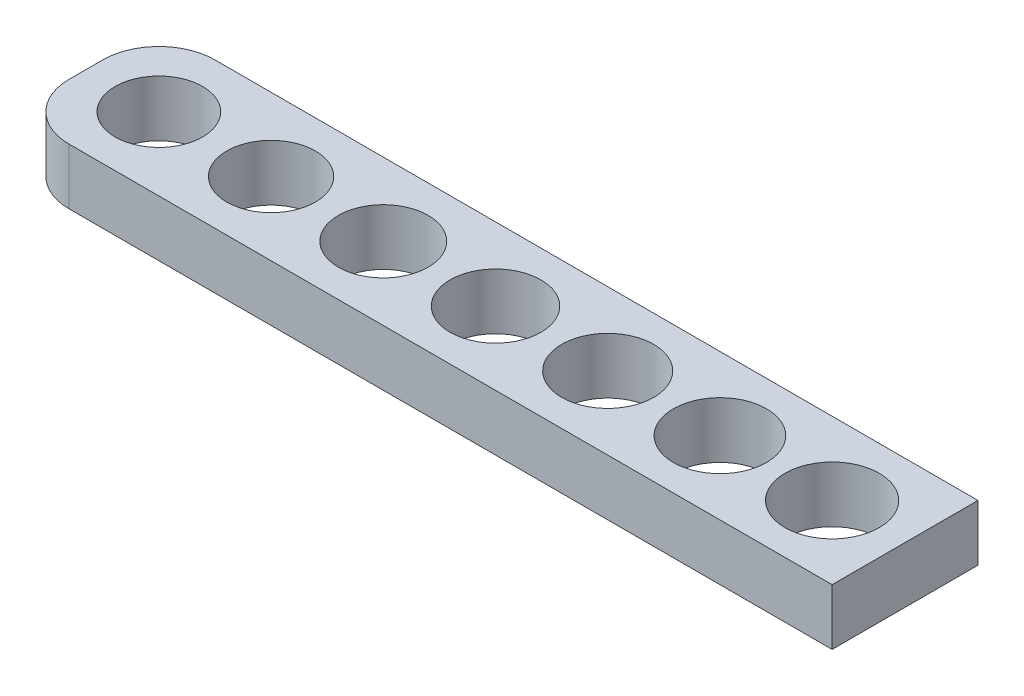
SolidWorks part; units mm, degrees
ref_plane "Front Plane" through (0, 0, 0) normal (0, 0, 1) x (1, 0, 0)
ref_plane "Top Plane" through (0, 0, 0) normal (0, 1, 0) x (1, 0, 0)
ref_plane "Right Plane" through (0, 0, 0) normal (1, 0, 0) x (0, 0, -1)
sketch "Sketch2" plane through (0, 0, 0) normal (0, 1, 0) x (1, 0, 0)
  line L0 (0, 0) -> (10, 0) construction
  line L1 (10, 0) -> (20, 0) construction
  line L2 (20, 0) -> (30, 0) construction
  line L3 (30, 0) -> (40, 0) construction
  line L4 (40, 0) -> (50, 0) construction
  line L5 (50, 0) -> (60, 0) construction
  line L7 (-6.5, -6.5) -> (66.5, -6.5)
  line L8 (-6.5, -6.5) -> (-6.5, 6.5)
  line L9 (-6.5, 6.5) -> (66.5, 6.5)
  line L10 (66.5, -6.5) -> (66.5, 6.5)
  circle A0 centre (0, 0) radius 3.9
  circle A1 centre (10, 0) radius 3.95
  circle A2 centre (20, 0) radius 4
  circle A3 centre (30, 0) radius 4.05
  circle A4 centre (40, 0) radius 4.1
  circle A5 centre (50, 0) radius 4.15
  circle A6 centre (60, 0) radius 4.2
  dimension "D2" = 7.8
  dimension "D3" = 7.9
  dimension "D4" = 8
  dimension "D5" = 8.1
  dimension "D6" = 8.2
  dimension "D7" = 8.3
  dimension "D8" = 8.4
  dimension "D9" = 6.5
  dimension "D1" = 10
  dimension "D10" = 6.5
  dimension "D11" = 6.5
  dimension "D12" = 6.5
extrude "Boss-Extrude1" add sketch "Sketch2" along normal blind 5
fillet "Fillet1" radius 5 2 edges at (-6.5, 2.5, -6.5) (-6.5, 2.5, 6.5)
